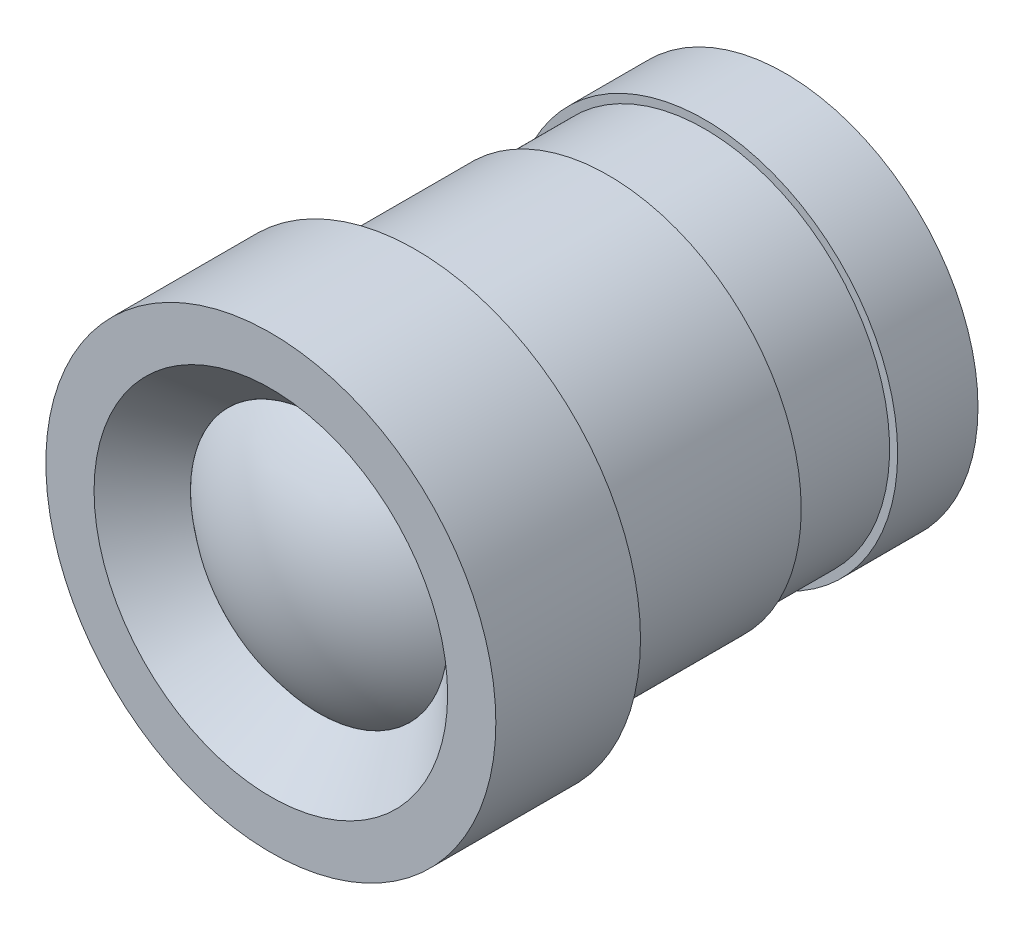
SolidWorks part; units mm, degrees
ref_plane "Front Plane" through (0, 0, 0) normal (0, 0, 1) x (1, 0, 0)
ref_plane "Top Plane" through (0, 0, 0) normal (0, 1, 0) x (1, 0, 0)
ref_plane "Right Plane" through (0, 0, 0) normal (1, 0, 0) x (0, 0, -1)
sketch "Sketch1" plane through (0, 0, 0) normal (1, 0, 0) x (0, 0, -1)
  line L0 (-1.5, 0) -> (14.5, 0) construction
  line L1 (-1.5, 0) -> (-1.5, 7)
  line L2 (-1.5, 7) -> (3, 7)
  line L3 (3, 7) -> (3, 6)
  line L4 (3, 6) -> (14.5, 6)
  line L5 (-1.5, 0) -> (14.5, 0)
  line L9 (14.5, 6) -> (14.5, 0)
  point P4 (0, 0)
  point P17 (3, 6.5)
  dimension "D1" = 16
  dimension "D2" = 14
  dimension "D3" = 4.5
  dimension "D4" = 12
  dimension "D5" = 1.5
revolve "Revolve1" add sketch "Sketch1" angle 360 about L0
sketch "Sketch2" plane through (0, 0, 1.5) normal (0, 0, 1) x (1, 0, 0)
  circle A2 centre (0, 0) radius 5.5
  circle A3 centre (0, 0) radius 5.5
  dimension "D1" = 1.5
extrude "Cut-Extrude1" cut sketch "Sketch2" against normal blind 1.5 draft 45
sketch "Sketch3" plane through (0, 0, 0) normal (0, 0, 1) x (1, 0, 0)
  circle A1 centre (0, 0) radius 4
  circle A2 centre (0, 0) radius 4
  dimension "D1" = 0
extrude "Cut-Extrude2" cut sketch "Sketch3" against normal through all
sketch "Sketch4" plane through (0, 0, 0) normal (0, 1, 0) x (1, 0, 0)
  line L0 (0, -1.5) -> (0, 14.5) construction
  line L1 (4, 14.5) -> (-4, 14.5) construction
  line L2 (4, 0) -> (4, 14.5)
  line L3 (6, 14.5) -> (-6, 14.5) construction
  line L4 (-5.5, -1.5) -> (5.5, -1.5) construction
  line L5 (4, 0) -> (-4, 0) construction
  line L6 (4, 14.5) -> (0, 14.5)
  line L7 (0, 14.5) -> (0, -1.5)
  arc A0 (4, 0) -> (0, -1.5) centre (0, 4.5833) cw
  dimension "D1" = 4
  dimension "D2" = 1.5
  dimension "D3" = 14.5
revolve "Revolve3" add sketch "Sketch4" angle 360 about L0
sketch "Sketch6" plane through (0, 0, -14.5) normal (0, 0, -1) x (-1, 0, 0)
  circle A0 centre (0, 0) radius 6 construction
  circle A1 centre (0, 0) radius 6
  circle A2 centre (0, 0) radius 5.75
  dimension "D1" = 0.25
extrude "Cut-Extrude3" cut sketch "Sketch6" against normal blind 3 from offset 2.5
